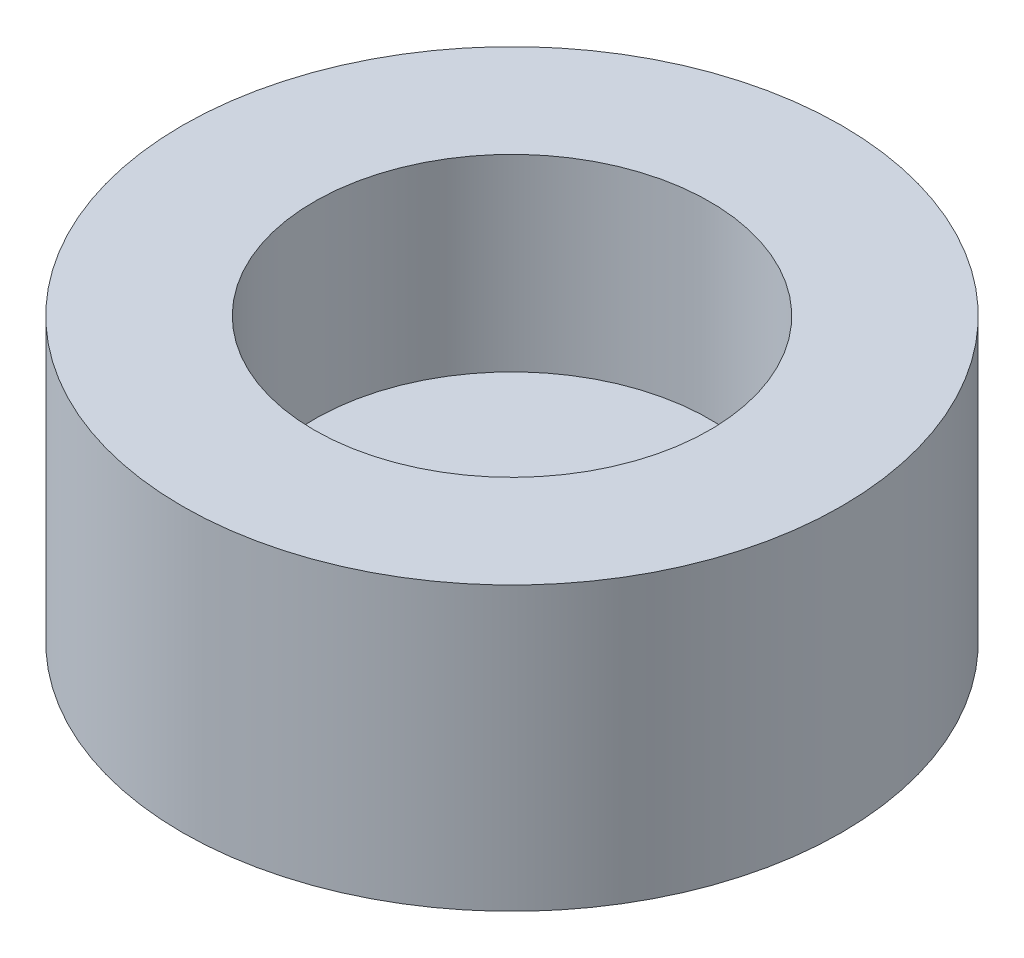
SolidWorks part; units mm, degrees
ref_plane "Front Plane" through (0, 0, 0) normal (0, 0, 1) x (1, 0, 0)
ref_plane "Top Plane" through (0, 0, 0) normal (0, 1, 0) x (1, 0, 0)
ref_plane "Right Plane" through (0, 0, 0) normal (1, 0, 0) x (0, 0, -1)
sketch "Sketch1" plane through (0, 0, 0) normal (0, 1, 0) x (1, 0, 0)
  circle A0 centre (0, 0) radius 3.5
  dimension "D1" = 7
extrude "Boss-Extrude1" add sketch "Sketch1" along normal blind 3
sketch "Sketch2" plane through (0, 3, 0) normal (0, 1, 0) x (1, 0, 0)
  circle A0 centre (0, 0) radius 2.1
  dimension "D1" = 4.2
extrude "Cut-Extrude1" cut sketch "Sketch2" against normal blind 2
